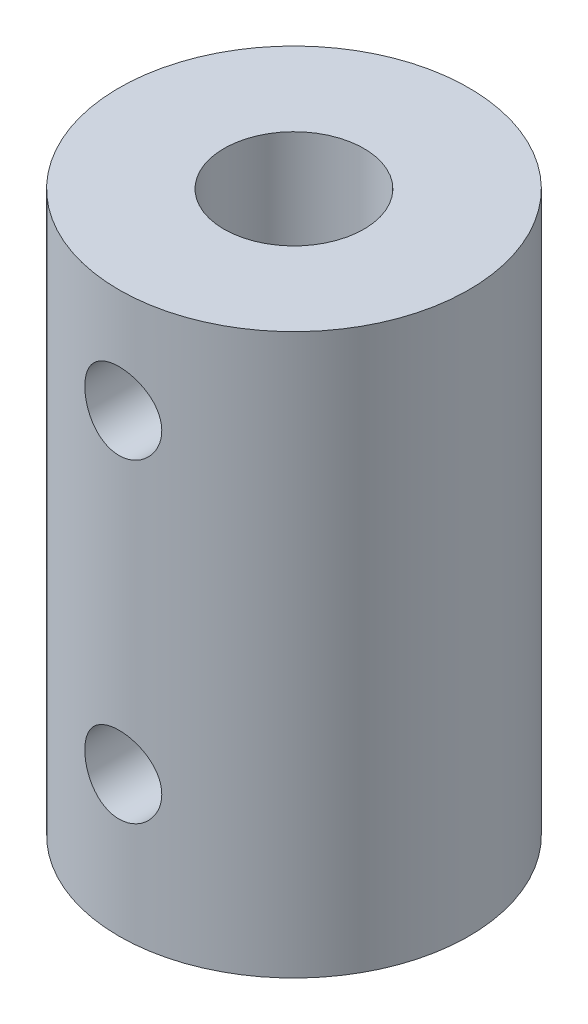
SolidWorks part; units mm, degrees
ref_plane "Front Plane" through (0, 0, 0) normal (0, 0, 1) x (1, 0, 0)
ref_plane "Top Plane" through (0, 0, 0) normal (0, 1, 0) x (1, 0, 0)
ref_plane "Right Plane" through (0, 0, 0) normal (1, 0, 0) x (0, 0, -1)
sketch "Sketch1" plane through (0, 0, 0) normal (0, 1, 0) x (1, 0, 0)
  circle A0 centre (0, 0) radius 7.5
  dimension "D1" = 15
extrude "Boss-Extrude1" add sketch "Sketch1" against normal blind 24
sketch "Sketch6" plane through (0, 0, 0) normal (0, 1, 0) x (1, 0, 0)
  circle A0 centre (0, 0) radius 3
  dimension "D1" = 6
extrude "Cut-Extrude3" cut sketch "Sketch6" against normal blind 8
sketch "Sketch3" plane through (0, -24, 0) normal (0, -1, 0) x (1, 0, 0)
  circle A0 centre (0, 0) radius 4
  dimension "D1" = 8
extrude "Cut-Extrude2" cut sketch "Sketch3" against normal blind 12
hole_wizard "M4 Tapped Hole1" positions "3DSketch1" profile "Sketch4" tap size "M4" standard "ISO"
sketch3d "3DSketch1"
  line L0 (0, 0, 7.5) -> (0, -24, 7.5) construction
  circle A0 centre (0, 0, 0) radius 7.5 construction
  circle A1 centre (0, -24, 0) radius 7.5 construction
  point P0 (0, -4.5, 7.5)
  point P14 (0, 7.5, 0)
  point P17 (0, -16.5, 0)
  point P31 (0, -18, 7.5)
  dimension "D1" = 4.5
  dimension "D2" = 6
cosmetic thread "Hole Thread1" parameters "D2"=4
cosmetic thread "Hole Thread2" parameters "D2"=4
sketch "Sketch4" plane through (0, -4.5, 7.5) normal (1, 0, 0) x (0, -1, 0)
  line L0 (0, 0) -> (0, 4.5)
  line L1 (0, 4.5) -> (1.65, 4.5)
  line L2 (1.65, 4.5) -> (1.65, 0)
  line L5 (1.65, 0) -> (0, 0)
  line L11 (0, -6.35) -> (0, 107.95) construction
  dimension "Thru Tap Drill Dia." = 3.3
  dimension "Thru Tap Drill Depth" = 4.5
